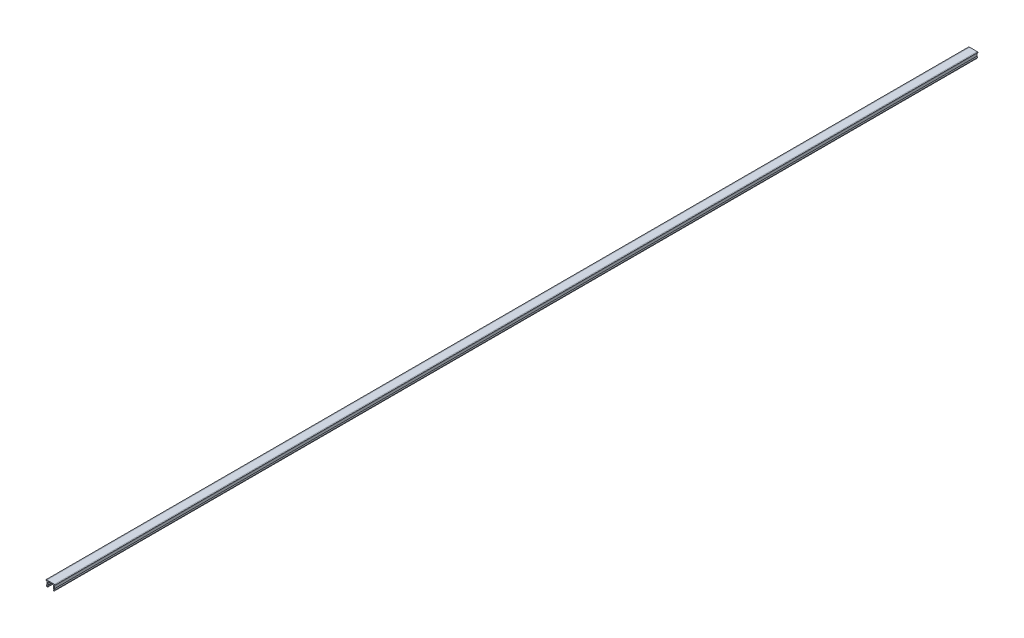
SolidWorks part; units mm, degrees
material "Пластик"
ref_plane "Спереди" through (0, 0, 0) normal (0, 0, 1) x (1, 0, 0)
ref_plane "Сверху" through (0, 0, 0) normal (0, 1, 0) x (1, 0, 0)
ref_plane "Справа" through (0, 0, 0) normal (1, 0, 0) x (0, 0, -1)
sketch "Эскиз1" plane through (0, 0, 0) normal (0, 0, 1) x (1, 0, 0)
  line L21 (-4.1, 0) -> (-5, -0.1587)
  line L22 (-5, -0.1587) -> (-5, -0.8)
  line L23 (-5, -0.8) -> (-4.1, -0.8)
  line L24 (-4.1, -0.8) -> (-4.1, -4.1962)
  line L25 (-4.1, -4.1962) -> (-4.6877, -5.2141)
  line L26 (-4.6877, -5.2141) -> (-4.1, -6.2321)
  line L27 (-3.1, -5.9641) -> (-3.533, -5.2141)
  line L28 (-3.533, -5.2141) -> (-3.1, -4.4641)
  line L29 (-3.1, -4.4641) -> (-3.1, -1)
  line L30 (-3.1, -1) -> (3.1, -1)
  line L31 (-4.1, 0) -> (4.1, 0)
  line L32 (0, 0) -> (0, -1) construction
  line L33 (3.1, -4.4641) -> (3.1, -1)
  line L34 (3.533, -5.2141) -> (3.1, -4.4641)
  line L35 (3.1, -5.9641) -> (3.533, -5.2141)
  line L36 (4.6877, -5.2141) -> (4.1, -6.2321)
  line L37 (4.1, -4.1962) -> (4.6877, -5.2141)
  line L38 (4.1, -0.8) -> (4.1, -4.1962)
  line L39 (5, -0.8) -> (4.1, -0.8)
  line L40 (5, -0.1587) -> (5, -0.8)
  line L41 (4.1, 0) -> (5, -0.1587)
  arc A0 (-4.1, -6.2321) -> (-3.1, -5.9641) centre (-3.6359, -5.9641) ccw
  arc A1 (4.1, -6.2321) -> (3.1, -5.9641) centre (3.6359, -5.9641) cw
  point P2 (-2.361, -1.7969)
  point P28 (-2.5404, 0)
  point P29 (-2.1, -5.8959)
  point P30 (-1.9938, -7.2818)
  point P31 (-3.6877, -6.0654)
  point P32 (-2.1, -6.985)
  dimension "D1" = 10
  dimension "D2" = 8.2
  dimension "D3" = 6.5
  dimension "D4" = 150
  dimension "D5" = 120
  dimension "D6" = 1
  dimension "D7" = 1
  dimension "D8" = 1
  dimension "D9" = 0.8
  dimension "D10" = 1
  dimension "D11" = 10
  dimension "D12" = 1.5
extrude "Бобышка-Вытянуть1" add sketch "Эскиз1" along normal blind 1000
